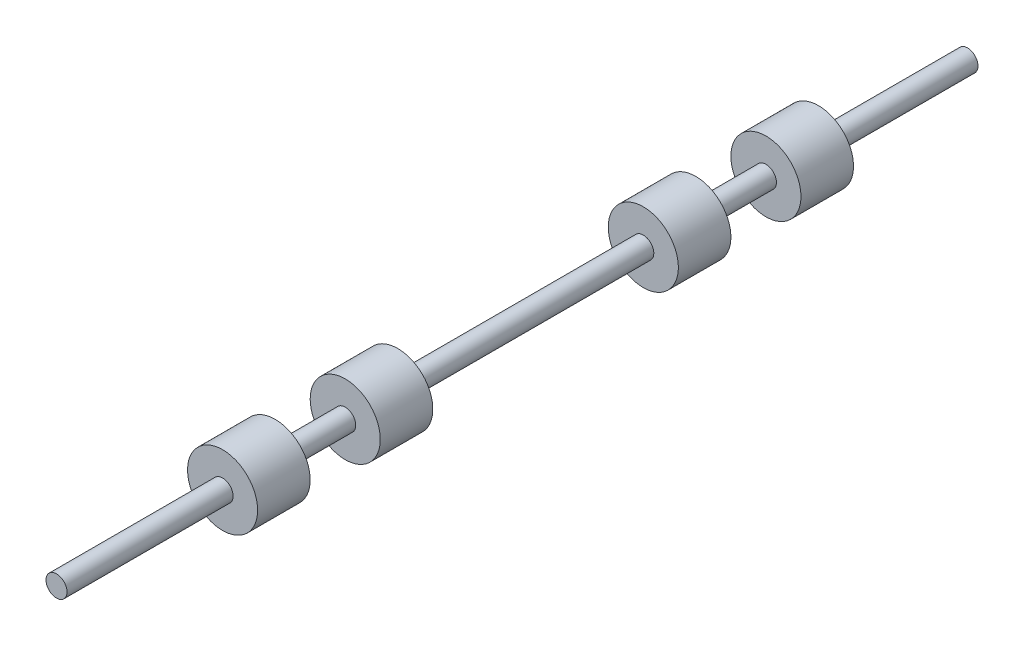
SolidWorks part; units mm, degrees
ref_plane "Front Plane" through (0, 0, 0) normal (0, 0, 1) x (1, 0, 0)
ref_plane "Top Plane" through (0, 0, 0) normal (0, 1, 0) x (1, 0, 0)
ref_plane "Right Plane" through (0, 0, 0) normal (1, 0, 0) x (0, 0, -1)
sketch "Sketch2" plane through (0, 0, 0) normal (0, 0, 1) x (1, 0, 0)
  circle A0 centre (0, 0) radius 0.3
  dimension "D1" = 0.6
extrude "Boss-Extrude1" add sketch "Sketch2" along normal blind 26
sketch "Sketch3" plane through (0, 0, 0) normal (0, 1, 0) x (1, 0, 0)
  line L0 (0, 0) -> (0, -26) construction
  line L1 (-0.3, -26) -> (0.3, -26) construction
  line L2 (0, -6.753) -> (5.6322, -6.753) construction
  line L3 (0, -4.253) -> (1, -4.253)
  line L4 (0, -4.253) -> (0, -5.753)
  line L5 (0, -5.753) -> (1, -5.753)
  line L6 (1, -4.253) -> (1, -5.753)
  line L7 (0, -7.753) -> (1, -7.753)
  line L8 (0, -7.753) -> (0, -9.253)
  line L9 (0, -9.253) -> (1, -9.253)
  line L10 (1, -7.753) -> (1, -9.253)
  line L11 (0, -18.76) -> (7.0918, -18.76) construction
  line L12 (0, -16.26) -> (1, -16.26)
  line L13 (0, -16.26) -> (0, -17.76)
  line L14 (0, -17.76) -> (1, -17.76)
  line L15 (1, -16.26) -> (1, -17.76)
  line L16 (0, -19.76) -> (1, -19.76)
  line L17 (0, -19.76) -> (0, -21.26)
  line L18 (0, -21.26) -> (1, -21.26)
  line L19 (1, -19.76) -> (1, -21.26)
  dimension "D1" = 1.5
  dimension "D2" = 1.5
  dimension "D3" = 1
  dimension "D4" = 2
  dimension "D5" = 1
  dimension "D6" = 1.5
  dimension "D7" = 1.5
  dimension "D8" = 2
  dimension "D9" = 1
  dimension "D10" = 1
  dimension "D11" = 12.007
  dimension "D12" = 7.24
revolve "Revolve1" add sketch "Sketch3" angle 360 about L0
